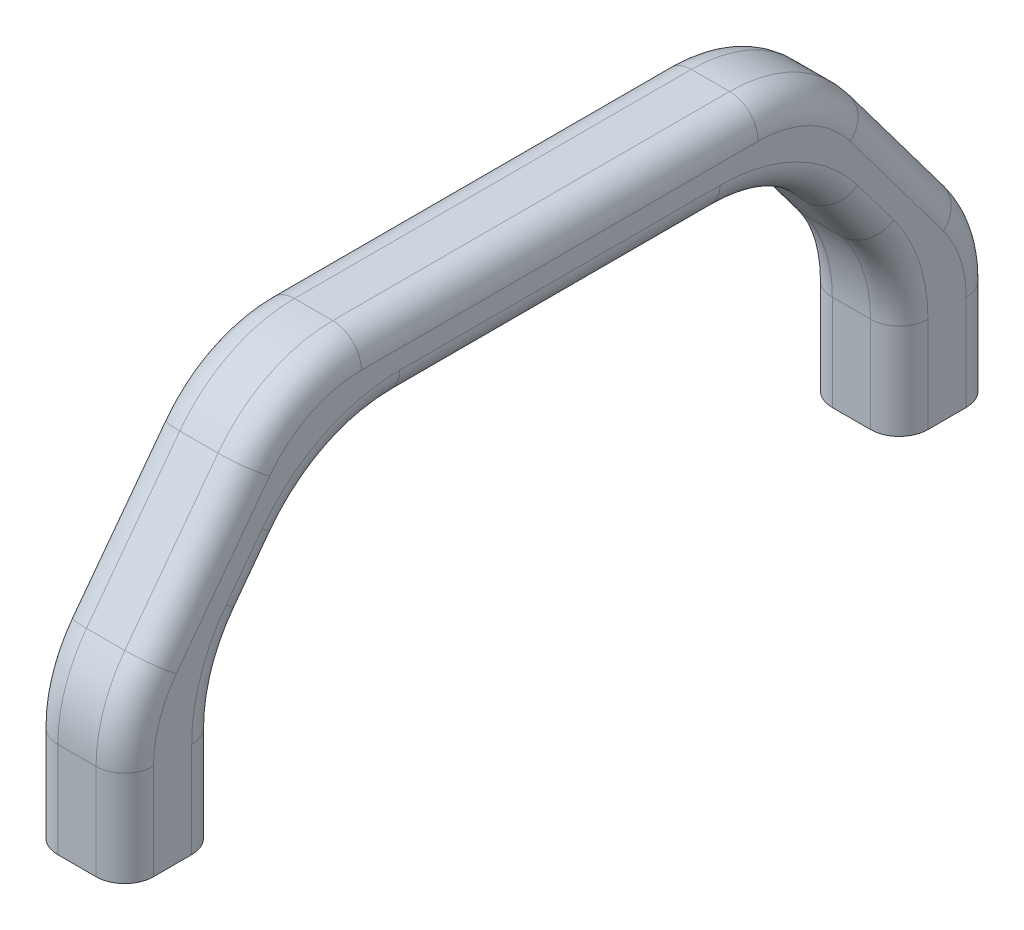
SolidWorks part; units mm, degrees
ref_plane "Front Plane" through (0, 0, 0) normal (0, 0, 1) x (1, 0, 0)
ref_plane "Top Plane" through (0, 0, 0) normal (0, 1, 0) x (1, 0, 0)
ref_plane "Right Plane" through (0, 0, 0) normal (1, 0, 0) x (0, 0, -1)
sketch "Sketch1" plane through (0, 0, 0) normal (0, 1, 0) x (1, 0, 0)
  line L1 (-6.5868, 45.5) -> (3.4132, 45.5)
  line L2 (-6.5868, 45.5) -> (-6.5868, 35.5)
  line L3 (-6.5868, 35.5) -> (3.4132, 35.5)
  line L4 (3.4132, 45.5) -> (3.4132, 35.5)
  line L5 (-6.5868, 45.5) -> (3.4132, 35.5) construction
  line L6 (-6.5868, 35.5) -> (3.4132, 45.5) construction
  line L7 (-6.5868, -35.5) -> (3.4132, -35.5)
  line L8 (-6.5868, -35.5) -> (-6.5868, -45.5)
  line L9 (-6.5868, -45.5) -> (3.4132, -45.5)
  line L10 (3.4132, -35.5) -> (3.4132, -45.5)
  line L11 (-6.5868, -35.5) -> (3.4132, -45.5) construction
  line L12 (-6.5868, -45.5) -> (3.4132, -35.5) construction
  circle A0 centre (-1.5868, 40.5) radius 1.6
  circle A1 centre (-1.5868, -40.5) radius 1.6
  dimension "D1" = 81
  dimension "D2" = 3.2
  dimension "D5" = 40.5
  dimension "D3" = 10
  dimension "D4" = 10
extrude "Boss-Extrude1" add sketch "Sketch1" along normal blind 15
sketch "Sketch4" plane through (3.4132, 0, 0) normal (1, 0, 0) x (0, 0, -1)
  line L0 (0, 0) -> (0, 30) construction
  line L1 (-35.5, 15) -> (-24.25, 30)
  line L2 (-24.25, 30) -> (24.25, 30)
  line L4 (28.25, 38) -> (-28.25, 38)
  line L5 (-28.25, 38) -> (-45.5, 15)
  line L6 (-45.5, 15) -> (-35.5, 15)
  line L7 (28.25, 38) -> (45.5, 15)
  line L8 (35.5, 15) -> (24.25, 30)
  line L9 (45.5, 15) -> (35.5, 15)
  line L10 (0, 38) -> (0, 40.4724) construction
  line L11 (-45.5, 0) -> (-35.5, 0) construction
  dimension "D1" = 8
  dimension "D2" = 8
  dimension "D3" = 38
extrude "Boss-Extrude2" add sketch "Sketch4" against normal blind 10
fillet "Fillet1" radius 15 8 edges at (-1.5868, 15, 35.5) (-1.5868, 15, 45.5) (-1.5868, 30, 24.25) (-1.5868, 38, 28.25) (-1.5868, 30, -24.25) (-1.5868, 15, -35.5) (-1.5868, 15, -45.5) (-1.5868, 38, -28.25)
fillet "Fillet2" radius 3 36 edges at (3.4132, 5, -45.5) (3.4132, 14.7434, -44.7302) (3.4132, 25.5, -37.625) (3.4132, 5, 45.5) (3.4132, 14.7434, 44.7302) (3.4132, 25.5, 37.625) (3.4132, 36.4164, 27.4582) (3.4132, 38, 0) (3.4132, 5, 35.5) (3.4132, 14.7434, 34.7302) (3.4132, 21.5, 30.625) (3.4132, 28.4164, 23.4582) (3.4132, 30, 0) (3.4132, 28.4164, -23.4582) (3.4132, 5, -35.5) (3.4132, 14.7434, -34.7302) (-6.5868, 5, 35.5) (-6.5868, 14.7434, 34.7302) (-6.5868, 21.5, 30.625) (-6.5868, 28.4164, 23.4582) (-6.5868, 30, 0) (-6.5868, 28.4164, -23.4582) (-6.5868, 21.5, -30.625) (-6.5868, 14.7434, -34.7302) (-6.5868, 5, -35.5) (-6.5868, 5, -45.5) (-6.5868, 14.7434, -44.7302) (-6.5868, 25.5, -37.625) (-6.5868, 36.4164, -27.4582) (-6.5868, 38, 0) (-6.5868, 36.4164, 27.4582) (-6.5868, 25.5, 37.625) (-6.5868, 14.7434, 44.7302) (-6.5868, 5, 45.5) (3.4132, 36.4164, -27.4582) (3.4132, 21.5, -30.625)
